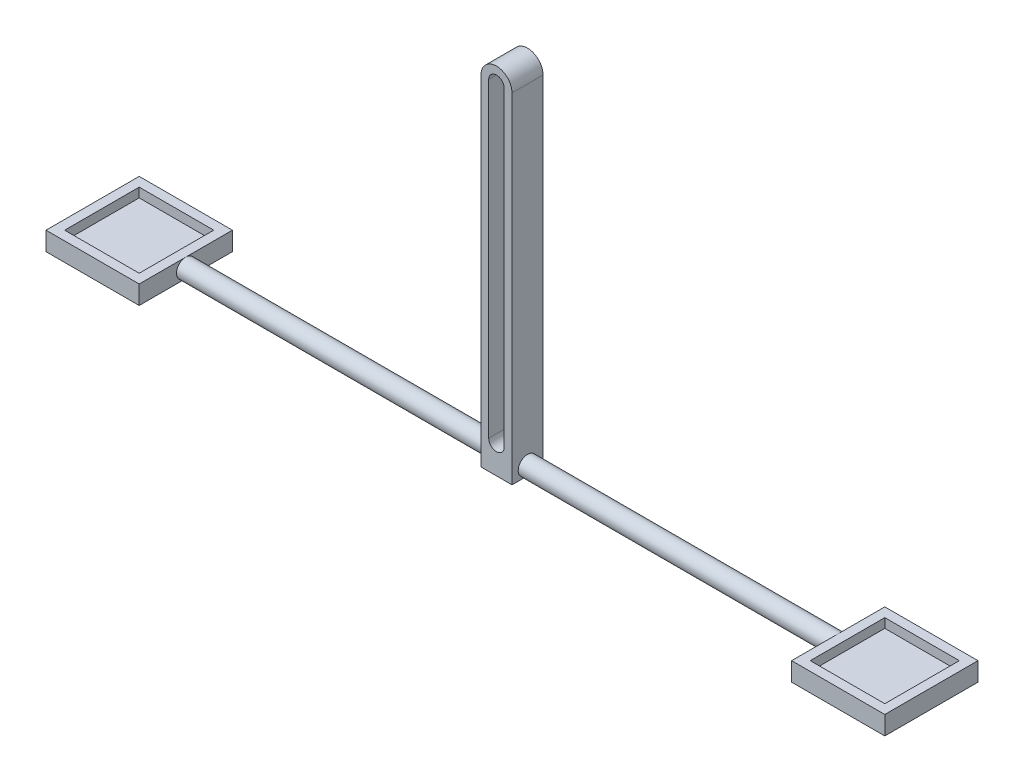
SolidWorks part; units mm, degrees
ref_plane "Front Plane" through (0, 0, 0) normal (0, 0, 1) x (1, 0, 0)
ref_plane "Top Plane" through (0, 0, 0) normal (0, 1, 0) x (1, 0, 0)
ref_plane "Right Plane" through (0, 0, 0) normal (1, 0, 0) x (0, 0, -1)
sketch "Sketch1" plane through (0, 0, 0) normal (0, 0, 1) x (1, 0, 0)
  line L0 (0, 0) -> (0, 100) construction
  line L1 (-2.5, 0) -> (-2.5, 100)
  line L2 (2.5, 0) -> (2.5, 100)
  line L3 (0, 100) -> (0, 0) construction
  line L4 (5, 100) -> (5, 0)
  line L5 (-5, 100) -> (-5, 0)
  line L6 (-5, 0) -> (-5, -10)
  line L7 (-5, -10) -> (5, -10)
  line L8 (5, -10) -> (5, 0)
  arc A0 (-2.5, 0) -> (2.5, 0) centre (0, 0) ccw
  arc A1 (2.5, 100) -> (-2.5, 100) centre (0, 100) ccw
  arc A2 (5, 100) -> (-5, 100) centre (0, 100) ccw
  point P2 (0, 50)
  point P7 (0, 50)
  point P14 (0, 105)
  point P17 (0, -10)
  dimension "D1" = 115
  dimension "D2" = 10
extrude "Boss-Extrude2" add sketch "Sketch1" along normal blind 10
sketch "Sketch3" plane through (5, 0, 0) normal (1, 0, 0) x (0, 0, -1)
  line L0 (-10, -10) -> (-10, -2.5) construction
  line L1 (-10, -2.5) -> (0, -2.5) construction
  line L2 (0, -2.5) -> (0, -10) construction
  line L3 (0, -10) -> (-10, -10) construction
  line L4 (-5, -10) -> (-5, -7.5) construction
  line L5 (-5, -7.5) -> (-5, -5) construction
  line L6 (-5, -5) -> (-5, -2.5) construction
  line L7 (-5, -7.5) -> (-10, -7.5) construction
  line L8 (-5, -7.5) -> (0, -7.5) construction
  circle A0 centre (-5, -6.25) radius 3
extrude "Boss-Extrude3" add sketch "Sketch3" along normal blind 100 and the other way blind 110
ref_plane "Plane1" through (0, -9.25, 0) normal (0, -1, 0) x (-1, 0, 0)
sketch "Sketch6" plane through (0, -9.25, 0) normal (0, -1, 0) x (-1, 0, 0)
  line L0 (-105, -2) -> (-105, 10)
  line L1 (-105, 10) -> (-135, 10)
  line L2 (-135, 10) -> (-135, -20)
  line L3 (-105, -8) -> (-105, -20)
  line L4 (-105, -20) -> (-135, -20)
  line L5 (105, -2) -> (105, 10)
  line L6 (105, 10) -> (135, 10)
  line L7 (135, 10) -> (135, -20)
  line L8 (135, -20) -> (105, -20)
  line L9 (105, -20) -> (105, -8)
  line L10 (-105, -2) -> (-105, -8)
  line L11 (105, -8) -> (105, -2)
extrude "Boss-Extrude4" add sketch "Sketch6" against normal blind 3
sketch "Sketch7" plane through (0, -6.25, 0) normal (0, 1, 0) x (1, 0, 0)
  line L0 (-105, -2) -> (-105, 10)
  line L1 (-105, 10) -> (-135, 10)
  line L2 (-135, 10) -> (-105, 10) construction
  line L3 (-135, 10) -> (-135, -20)
  line L4 (-105, -20) -> (-135, -20) construction
  line L5 (-135, -20) -> (-105, -20)
  line L6 (-105, -20) -> (-105, -8)
  line L7 (-105, -8) -> (-105, -2)
  line L8 (-105, -2) -> (-108, -2) construction
  line L9 (-108, -2) -> (-108, 7)
  line L10 (-108, 7) -> (-132, 7)
  line L11 (-132, 7) -> (-132, -17)
  line L12 (-132, -17) -> (-108, -17)
  line L13 (-108, -17) -> (-108, -8)
  line L14 (-108, -8) -> (-108, -2)
sketch "Sketch8" plane through (0, -6.25, 0) normal (0, 1, 0) x (1, 0, 0)
  line L6 (105, -2) -> (108, -2) construction
  line L7 (135, -2) -> (135, 10)
  line L8 (135, 10) -> (105, 10)
  line L9 (105, 10) -> (105, -20)
  line L10 (105, -20) -> (135, -20)
  line L11 (135, -20) -> (135, -8)
  line L12 (135, -8) -> (135, -2)
  line L13 (135, -2) -> (132, -2) construction
  line L14 (132, -2) -> (132, 7)
  line L15 (132, 7) -> (108, 7)
  line L16 (108, 7) -> (108, -17)
  line L17 (108, -17) -> (132, -17)
  line L18 (132, -17) -> (132, -8)
  line L19 (132, -8) -> (132, -2)
  line L20 (105, -8) -> (105, -2) construction
  line L21 (135, -20) -> (105, -20) construction
  line L22 (105, 10) -> (135, 10) construction
extrude "Boss-Extrude5" add sketch "Sketch7" along normal blind 3
extrude "Boss-Extrude6" add sketch "Sketch8" along normal blind 3
sketch "Sketch9" plane through (0, 0, 10) normal (0, 0, 1) x (1, 0, 0)
  line L0 (-19.2645, -9.25) -> (19.2645, -9.25) construction
  line L1 (-5, -10) -> (5, -10)
  line L2 (-5, -10) -> (-5, -9.25)
  line L3 (-5, -9.25) -> (5, -9.25)
  line L4 (5, -10) -> (5, -9.25)
extrude "Cut-Extrude1" cut sketch "Sketch9" against normal up to next
